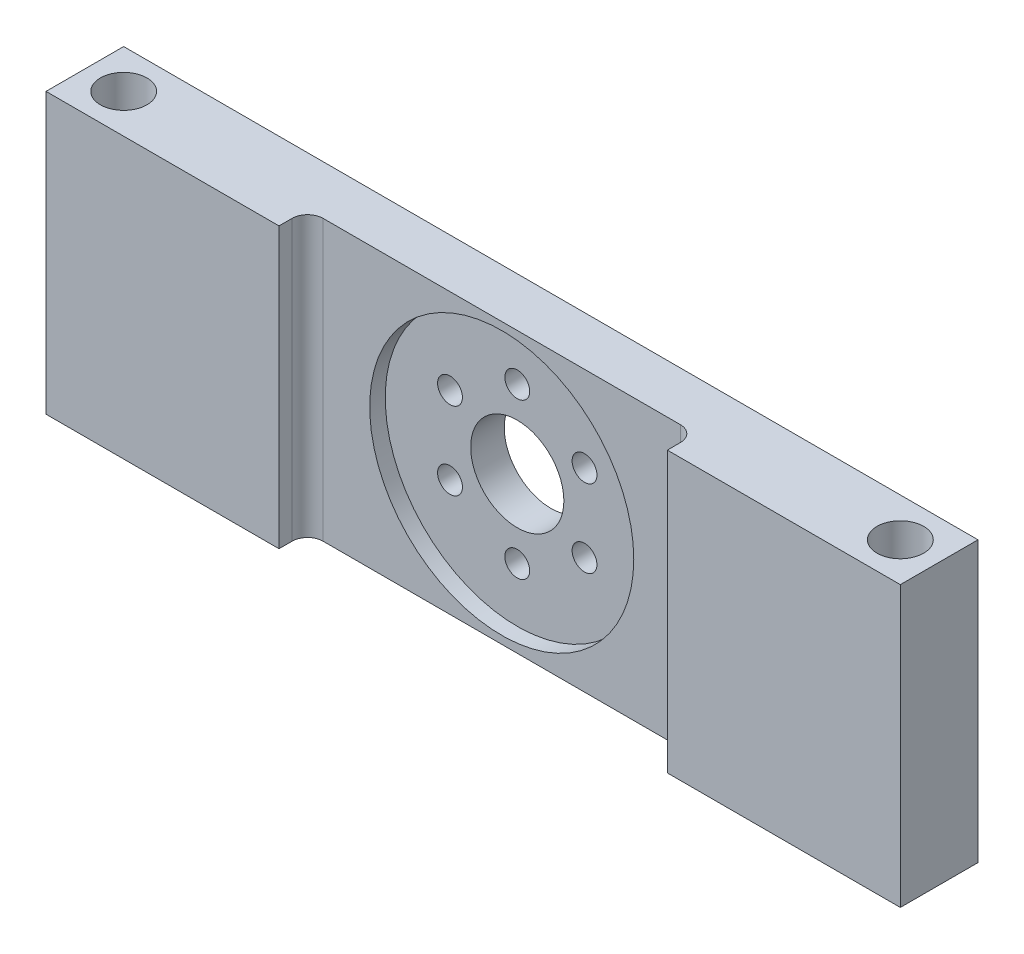
SolidWorks part; units mm, degrees
ref_plane "Front Plane" through (0, 0, 0) normal (0, 0, 1) x (1, 0, 0)
ref_plane "Top Plane" through (0, 0, 0) normal (0, 1, 0) x (1, 0, 0)
ref_plane "Right Plane" through (0, 0, 0) normal (1, 0, 0) x (0, 0, -1)
sketch "Sketch2" plane through (0, 0, 0) normal (0, 1, 0) x (1, 0, 0)
  line L0 (-86.3094, 0) -> (99.5032, 0) construction
  line L1 (-46.4402, 3.161) -> (-46.4402, -8.532) construction
  line L2 (-33.9402, -1.839) -> (-18.9402, -1.839)
  line L3 (-73.9402, -1.839) -> (-73.9402, 3.161)
  line L4 (-73.9402, 3.161) -> (-18.9402, 3.161)
  line L5 (-18.9402, -1.839) -> (-18.9402, 3.161)
  line L6 (-58.9402, -1.839) -> (-58.9402, 0)
  line L7 (-33.9402, -1.839) -> (-33.9402, 0)
  line L8 (-58.9402, 0) -> (-33.9402, 0)
  line L9 (-73.9402, -1.839) -> (-58.9402, -1.839)
  point P3 (0, 0)
  dimension "D1" = 55
  dimension "D2" = 5
  dimension "D3" = 15
  dimension "D4" = 15
extrude "Boss-Extrude1" add sketch "Sketch2" along normal blind 18
sketch "Sketch9" plane through (0, 0, 0) normal (0, 0, 1) x (1, 0, 0)
  line L0 (-46.4402, 18) -> (-46.4402, 0) construction
  line L1 (-58.9402, 18) -> (-33.9402, 18) construction
  line L2 (-58.9402, 0) -> (-33.9402, 0) construction
  circle A0 centre (-46.4402, 9) radius 8.5
  dimension "D1" = 17
extrude "Cut-Extrude6" cut sketch "Sketch9" against normal blind 1
sketch "Sketch10" plane through (0, 0, -1) normal (0, 0, 1) x (1, 0, 0)
  line L0 (-46.4402, 17.5) -> (-46.4402, 0.5) construction
  circle A0 centre (-46.4402, 9) radius 8.5 construction
  circle A1 centre (-46.4402, 9) radius 8.5 construction
  circle A2 centre (-46.4402, 9) radius 3
  dimension "D1" = 6
extrude "Cut-Extrude7" cut sketch "Sketch10" against normal through all
sketch "Sketch11" plane through (0, 0, -1) normal (0, 0, 1) x (1, 0, 0)
  line L0 (-46.4402, 17.5) -> (-46.4402, 0.5) construction
  circle A0 centre (-46.4402, 9) radius 8.5 construction
  circle A1 centre (-46.4402, 9) radius 8.5 construction
  circle A2 centre (-46.4402, 9) radius 5
  circle A3 centre (-46.4402, 14) radius 0.8
  circle A4 centre (-42.1101, 11.5) radius 0.8
  circle A5 centre (-46.4402, 9) radius 5
  circle A6 centre (-42.1101, 6.5) radius 0.8
  circle A7 centre (-46.4402, 9) radius 5
  circle A8 centre (-46.4402, 4) radius 0.8
  circle A9 centre (-46.4402, 9) radius 5
  circle A10 centre (-50.7704, 6.5) radius 0.8
  circle A11 centre (-46.4402, 9) radius 5
  circle A16 centre (-50.7704, 11.5) radius 0.8
  circle A17 centre (-46.4402, 9) radius 5
  point P36 (-46.4402, 9)
  dimension "D1" = 10
  dimension "D2" = 1.6
  dimension "D3" = 6
extrude "Cut-Extrude8" cut sketch "Sketch11" against normal through all
fillet "Fillet1" radius 1 2 edges at (-33.9402, 9, 0) (-58.9402, 9, 0)
sketch "Sketch13" plane through (0, 18, 0) normal (0, 1, 0) x (1, 0, 0)
  line L0 (-18.9402, 3.161) -> (-73.9402, 3.161) construction
  line L1 (-73.9402, 3.161) -> (-73.9402, -1.839) construction
  circle A0 centre (-71.4402, 0.661) radius 1.5
  circle A1 centre (-21.4402, 0.661) radius 1.5
  point P10 (-21.9587, 3.161)
  point P11 (-71.7405, 0.8342)
  dimension "D1" = 3
  dimension "D4" = 3
  dimension "D2" = 2.5
  dimension "D3" = 2.5
extrude "Cut-Extrude10" cut sketch "Sketch13" against normal through all
